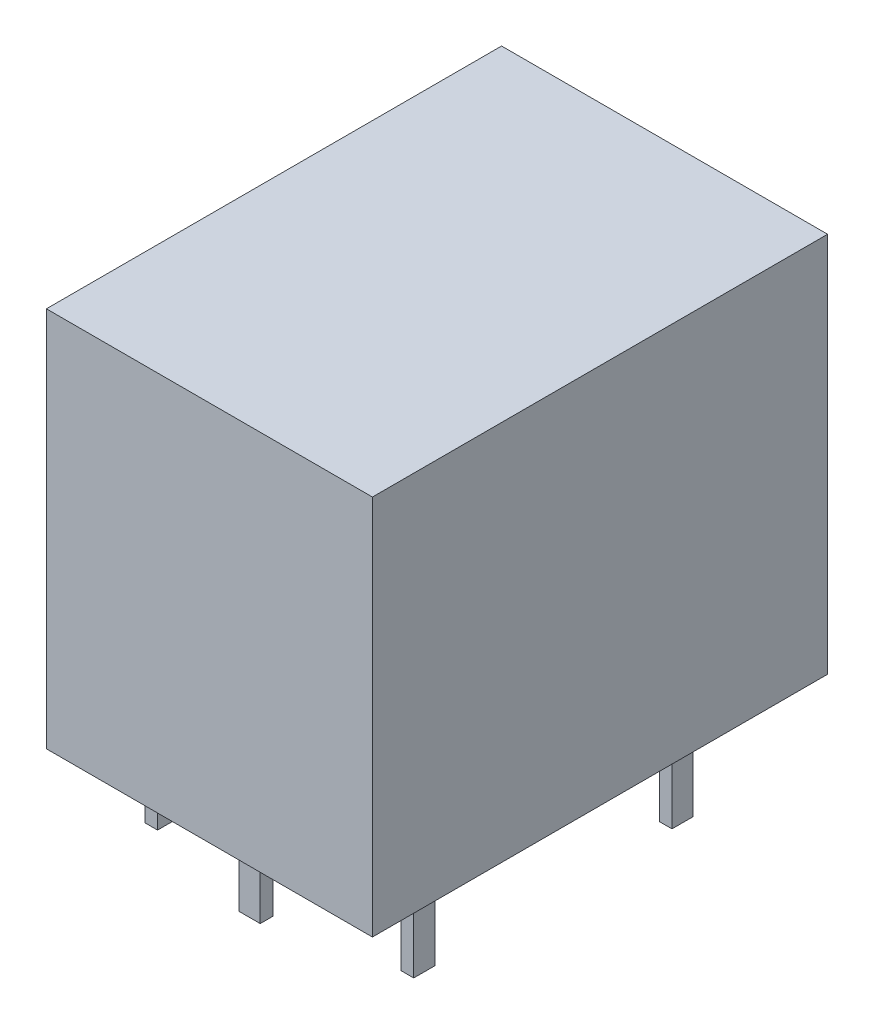
SolidWorks part; units mm, degrees
ref_plane "Front Plane" through (0, 0, 0) normal (0, 0, 1) x (1, 0, 0)
ref_plane "Top Plane" through (0, 0, 0) normal (0, 1, 0) x (1, 0, 0)
ref_plane "Right Plane" through (0, 0, 0) normal (1, 0, 0) x (0, 0, -1)
sketch "Sketch1" plane through (0, 0, 0) normal (0, 1, 0) x (1, 0, 0)
  line L1 (-7.7, 10.75) -> (7.7, 10.75)
  line L2 (-7.7, 10.75) -> (-7.7, -10.75)
  line L3 (-7.7, -10.75) -> (7.7, -10.75)
  line L4 (7.7, 10.75) -> (7.7, -10.75)
  line L5 (-7.7, 10.75) -> (7.7, -10.75) construction
  line L6 (-7.7, -10.75) -> (7.7, 10.75) construction
  point P0 (0, 0)
  dimension "D1" = 15.4
  dimension "D2" = 21.5
extrude "Boss-Extrude1" add sketch "Sketch1" along normal blind 18
sketch "Sketch2" plane through (0, 0, 0) normal (0, -1, 0) x (1, 0, 0)
  line L0 (7.7, -10.75) -> (-7.7, -10.75) construction
  line L1 (-6.35, -4.75) -> (-5.75, -4.75)
  line L2 (-6.35, -4.75) -> (-6.35, -5.75)
  line L3 (-6.35, -5.75) -> (-5.75, -5.75)
  line L4 (-5.75, -4.75) -> (-5.75, -5.75)
  line L5 (-6.35, 7.45) -> (-5.75, 7.45)
  line L6 (-6.35, 7.45) -> (-6.35, 6.45)
  line L7 (-6.35, 6.45) -> (-5.75, 6.45)
  line L8 (-5.75, 7.45) -> (-5.75, 6.45)
  line L9 (-0.5, 8.85) -> (0.5, 8.85)
  line L10 (-0.5, 8.85) -> (-0.5, 8.25)
  line L11 (-0.5, 8.25) -> (0.5, 8.25)
  line L12 (0.5, 8.85) -> (0.5, 8.25)
  line L13 (5.75, 7.45) -> (6.35, 7.45)
  line L14 (5.75, 7.45) -> (5.75, 6.45)
  line L15 (5.75, 6.45) -> (6.35, 6.45)
  line L16 (6.35, 7.45) -> (6.35, 6.45)
  line L17 (5.75, -4.75) -> (6.35, -4.75)
  line L18 (5.75, -4.75) -> (5.75, -5.75)
  line L19 (5.75, -5.75) -> (6.35, -5.75)
  line L20 (6.35, -4.75) -> (6.35, -5.75)
  line L21 (-7.7, 10.75) -> (7.7, 10.75) construction
  line L22 (-5.75, -5.75) -> (5.75, -5.75) construction
  point P20 (0, 8.85)
  point P27 (0, -5.75)
  point P28 (0, 0)
  dimension "D1" = 0.6
  dimension "D2" = 1
  dimension "D3" = 5
  dimension "D4" = 11.2
  dimension "D5" = 1.9
  dimension "D6" = 11.5
extrude "Boss-Extrude2" add sketch "Sketch2" along normal blind 4 separate body
